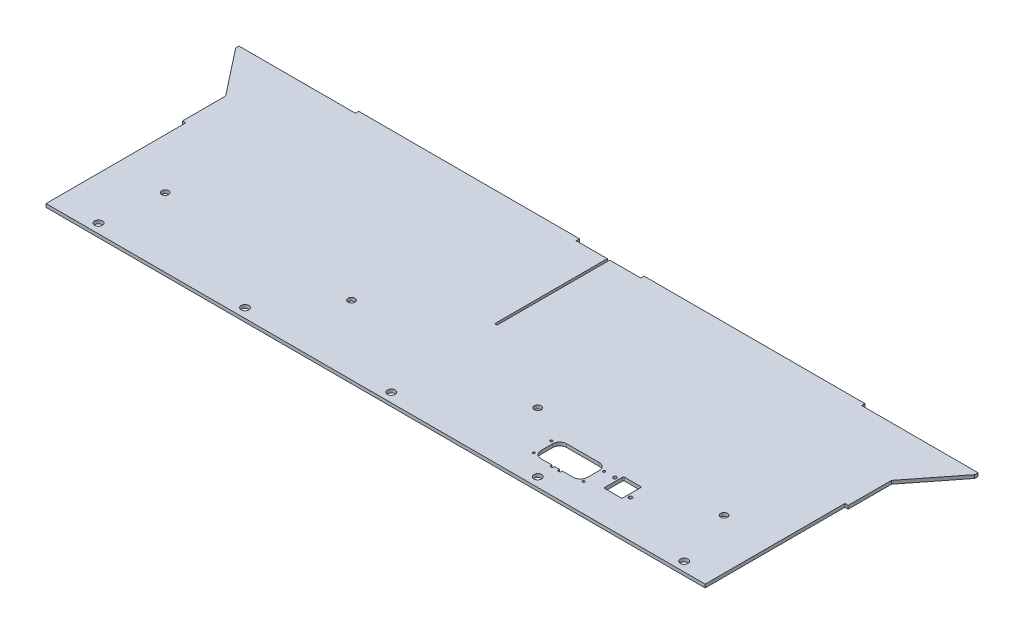
SolidWorks part; units mm, degrees
material "6061-T6 (SS)"
ref_plane "X-Y Datum" through (0, 0, 0) normal (0, 0, 1) x (1, 0, 0)
ref_plane "X-Z Datum" through (0, 0, 0) normal (0, 1, 0) x (1, 0, 0)
ref_plane "Y-Z Datum" through (0, 0, 0) normal (1, 0, 0) x (0, 0, -1)
sketch "Sketch1" plane through (0, 0, 0) normal (0, 1, 0) x (1, 0, 0)
  line L1 (-317.6778, 111.125) -> (317.6778, 111.125)
  line L2 (-317.6778, 111.125) -> (-317.6778, -111.125)
  line L3 (-317.6778, -111.125) -> (317.6778, -111.125)
  line L4 (317.6778, 111.125) -> (317.6778, -111.125)
  line L5 (-317.6778, 111.125) -> (317.6778, -111.125) construction
  line L6 (-317.6778, -111.125) -> (317.6778, 111.125) construction
  point P0 (0, 0)
  dimension "D1" = 635.3556
  dimension "D2" = 222.25
extrude "Boss-Extrude1" add sketch "Sketch1" along normal mid plane 3.175
sketch "Sketch3" plane through (0, 1.5875, 0) normal (0, 1, 0) x (1, 0, 0)
  line L0 (-317.6778, 111.125) -> (-352.6028, 111.125)
  line L1 (-352.6028, 111.125) -> (-352.6028, 107.95)
  line L2 (-352.6028, 107.95) -> (-317.6778, 63.5)
  line L3 (-317.6778, 111.125) -> (-317.6778, -111.125) construction
  line L16 (317.6778, -111.125) -> (317.6778, 111.125)
  line L17 (317.6778, 111.125) -> (-317.6778, 111.125)
  line L26 (-317.6778, 111.125) -> (-317.6778, -111.125)
  line L27 (-317.6778, -111.125) -> (317.6778, -111.125)
  line L38 (-317.6778, 111.125) -> (-317.6778, 63.5)
  line M26 (-317.6778, 111.125) -> (-317.6778, -111.125)
  dimension "D1" = 34.925
  dimension "D2" = 3.175
  dimension "D3" = 44.45
  dimension "D4" = 0
extrude "Boss-Extrude3" add sketch "Sketch3" against normal blind 3.175 contours L1 L2 L0 M26
mirror "Mirror1" about plane through (0, 0, 0) normal (1, 0, 0) of "Boss-Extrude3"
sketch "Sketch4" plane through (0, 1.5875, 0) normal (0, 1, 0) x (1, 0, 0)
  line L0 (-273.2278, -111.125) -> (-273.2278, -102.235)
  line L1 (-317.6778, -111.125) -> (317.6778, -111.125) construction
  line L2 (-273.2278, -102.235) -> (-317.6778, -102.235)
  line L3 (-317.6778, 63.5) -> (-317.6778, -111.125) construction
  circle A0 centre (-273.2278, -102.235) radius 3.675
extrude "Cut-Extrude1" cut sketch "Sketch4" against normal blind 10 contours L0 A0 L2 | L2 A0 L0
pattern_linear "LPattern1" count 5 spacing 139.7 along (1, 0, 0) of "Cut-Extrude1"
sketch "Sketch6" plane through (0, 1.5875, 0) normal (0, 1, 0) x (1, 0, 0)
  line L0 (0, -191.7444) -> (0, 191.7444) construction
  line L1 (317.6778, -111.125) -> (314.5028, -111.125)
  line L2 (317.6778, -111.125) -> (317.6778, 22.225)
  line L3 (317.6778, 22.225) -> (314.5028, 22.225)
  line L4 (314.5028, -111.125) -> (314.5028, 22.225)
  line L5 (-317.6778, -111.125) -> (-314.5028, -111.125)
  line L6 (-317.6778, 22.225) -> (-314.5028, 22.225)
  line L7 (-317.6778, -111.125) -> (-317.6778, 22.225)
  line L8 (-314.5028, -111.125) -> (-314.5028, 22.225)
  line L9 (352.6028, 111.125) -> (-352.6028, 111.125) construction
  line L10 (1.143, 111.125) -> (-1.143, 111.125)
  line L11 (1.143, 111.125) -> (1.143, 3.683)
  line L12 (1.143, 3.683) -> (-1.143, 3.683)
  line L13 (-1.143, 111.125) -> (-1.143, 3.683)
  line L14 (0, 3.683) -> (0, 111.125) construction
  point P9 (0, 0)
  dimension "D1" = 3.175
  dimension "D2" = 133.35
  dimension "D3" = 107.442
  dimension "D4" = 2.286
extrude "Cut-Extrude2" cut sketch "Sketch6" against normal through all
sketch "Sketch8" plane through (0, 1.5875, 0) normal (0, 1, 0) x (1, 0, 0)
  line L0 (-314.5028, -111.125) -> (314.5028, -111.125) construction
  line L1 (314.5028, 22.225) -> (314.5028, -111.125) construction
  circle A0 centre (266.7, -45.2374) radius 3
  dimension "D3" = 6
  dimension "D1" = 65.8876
  dimension "D2" = 47.8028
hole_wizard "M6 Clearance Hole1" positions "Sketch9" profile "Sketch10" hole size "M6" standard "ANSI Metric" end condition through all
sketch "Sketch9" plane through (0, 1.5875, 0) normal (0, 1, 0) x (1, 0, 0)
  point P0 (266.7, -45.2374)
sketch "Sketch10" plane through (266.7, 1.5875, 45.2374) normal (1, 0, 0) x (0, 0, 1)
  line L0 (0, 0) -> (0, 3.175)
  line L1 (0, 3.175) -> (3.3, 3.175)
  line L2 (3.3, 3.175) -> (3.3, 0)
  line L5 (3.3, 0) -> (0, 0)
  line L11 (0, -6.35) -> (0, 107.95) construction
  dimension "Thru Hole Dia." = 6.6
  dimension "Thru Hole Depth" = 3.175
pattern_linear "LPattern2" count 4 spacing 177.8 along (-1, 0, 0) of "M6 Clearance Hole1"
sketch "Sketch12" plane through (0, 0, -111.125) normal (0, 0, -1) x (-1, 0, 0)
  line L0 (-352.6028, -1.5875) -> (-1.143, -1.5875) construction
  line L1 (-241.4778, -1.5875) -> (-30.8229, -1.5875)
  line L2 (-241.4778, -1.5875) -> (-241.4778, 1.5875)
  line L3 (-241.4778, 1.5875) -> (-30.8229, 1.5875)
  line L4 (-30.8229, -1.5875) -> (-30.8229, 1.5875)
  line L5 (-241.4778, -1.5875) -> (-241.4778, 1.5875) construction
  line L6 (-352.6028, 1.5875) -> (-1.143, 1.5875) construction
  line L7 (-30.8229, 1.5875) -> (-30.8229, -1.5875) construction
  line L8 (1.143, 1.5875) -> (352.6028, 1.5875) construction
  line L9 (30.8229, 1.5875) -> (241.4778, 1.5875)
  line L10 (30.8229, 1.5875) -> (30.8229, -1.5875)
  line L11 (30.8229, -1.5875) -> (241.4778, -1.5875)
  line L12 (241.4778, 1.5875) -> (241.4778, -1.5875)
  line L13 (30.8229, 1.5875) -> (30.8229, -1.5875) construction
  line L14 (1.143, -1.5875) -> (352.6028, -1.5875) construction
  line L15 (241.4778, -1.5875) -> (241.4778, 1.5875) construction
extrude "Boss-Extrude4" add sketch "Sketch12" along normal blind 3.175
sketch "Sketch13" plane through (0, 1.5875, 0) normal (0, 1, 0) x (1, 0, 0)
  line L1 (145.2142, -85.2806) -> (143.4142, -85.2806) construction
  line L4 (152.4142, -85.2806) -> (150.6142, -85.2806) construction
  line L12 (145.4974, -87.7806) -> (145.7599, -84.7806) construction
  line L21 (143.131, -87.7806) -> (145.4974, -87.7806) construction
  line L22 (187.8642, -80.0254) -> (202.8142, -80.0254)
  line L23 (203.9642, -78.8754) -> (203.9642, -62.4254)
  line L28 (202.8142, -61.2754) -> (187.8642, -61.2754)
  line L29 (186.7142, -62.4254) -> (186.7142, -78.8754)
  line L30 (187.8642, -80.0254) -> (202.8142, -80.0254)
  line L45 (203.9642, -78.8754) -> (203.9642, -62.4254)
  line L46 (202.8142, -61.2754) -> (187.8642, -61.2754)
  line L47 (186.7142, -62.4254) -> (186.7142, -78.8754)
  line L60 (142.8686, -84.7806) -> (143.131, -87.7806) construction
  line L62 (152.4142, -85.7806) -> (163.4142, -85.7806) construction
  line L72 (170.1142, -79.0806) -> (170.1142, -67.8806) construction
  line L241 (163.4142, -61.1806) -> (132.4142, -61.1806) construction
  line L242 (125.7142, -67.8806) -> (125.7142, -79.0806) construction
  line L243 (132.4142, -85.7806) -> (143.4142, -85.7806) construction
  line L244 (202.8142, -79.5254) -> (202.8142, -78.8754) construction
  line L245 (152.6974, -87.7806) -> (152.9599, -84.7806) construction
  line L246 (150.331, -87.7806) -> (152.6974, -87.7806) construction
  line L247 (150.0686, -84.7806) -> (150.331, -87.7806) construction
  line L248 (145.2142, -85.7806) -> (150.6142, -85.7806) construction
  line L249 (145.2142, -85.2806) -> (143.4142, -85.2806)
  line L250 (152.4142, -85.2806) -> (150.6142, -85.2806)
  line L251 (145.4974, -87.7806) -> (145.7599, -84.7806)
  line L252 (143.131, -87.7806) -> (145.4974, -87.7806)
  line L253 (142.8686, -84.7806) -> (143.131, -87.7806)
  line L254 (152.4142, -85.7806) -> (163.4142, -85.7806)
  line L255 (170.1142, -79.0806) -> (170.1142, -67.8806)
  line L256 (163.4142, -61.1806) -> (132.4142, -61.1806)
  line L257 (125.7142, -67.8806) -> (125.7142, -79.0806)
  line L258 (132.4142, -85.7806) -> (143.4142, -85.7806)
  line L259 (202.8142, -79.5254) -> (202.8142, -78.8754)
  line L260 (152.6974, -87.7806) -> (152.9599, -84.7806)
  line L261 (150.331, -87.7806) -> (152.6974, -87.7806)
  line L262 (150.0686, -84.7806) -> (150.331, -87.7806)
  line L263 (145.2142, -85.7806) -> (150.6142, -85.7806)
  arc A72 (163.4142, -85.7806) -> (170.1142, -79.0806) centre (163.4142, -79.0806) ccw construction
  arc A73 (170.1142, -67.8806) -> (163.4142, -61.1806) centre (163.4142, -67.8806) ccw construction
  arc A74 (132.4142, -61.1806) -> (125.7142, -67.8806) centre (132.4142, -67.8806) ccw construction
  arc A75 (125.7142, -79.0806) -> (132.4142, -85.7806) centre (132.4142, -79.0806) ccw construction
  arc A76 (163.4142, -85.7806) -> (170.1142, -79.0806) centre (163.4142, -79.0806) ccw
  arc A77 (170.1142, -67.8806) -> (163.4142, -61.1806) centre (163.4142, -67.8806) ccw
  arc A78 (132.4142, -61.1806) -> (125.7142, -67.8806) centre (132.4142, -67.8806) ccw
  arc A79 (125.7142, -79.0806) -> (132.4142, -85.7806) centre (132.4142, -79.0806) ccw
  spline S8 degree 3 poles (-1500.8883, -4778.2266) (166.1174, 186.6721) (190.3999, -88.1059) (203.6527, -79.7139) (212.0447, -66.4612) (-62.7298, -42.1789) (4902.0719, 1624.7958) knots -23.26266 -23.26266 -23.26266 -23.26266 0.25 0.5 0.75 24.262513 24.262513 24.262513 24.262513 only from (202.8142, -80.0254) to (203.9642, -78.8754)
  spline S9 degree 3 poles (4902.1654, -1766.128) (-62.7333, -99.1222) (212.0448, -74.8397) (203.6527, -61.5869) (190.4, -53.1949) (166.1177, -327.9695) (-1500.8569, 4636.8323) knots -23.26266 -23.26266 -23.26266 -23.26266 0.25 0.5 0.75 24.262513 24.262513 24.262513 24.262513 only from (203.9642, -62.4254) to (202.8142, -61.2754)
  spline S10 degree 3 poles (1891.5668, 4636.9258) (224.5611, -327.9729) (200.2785, -53.1948) (187.0258, -61.5869) (178.6337, -74.8396) (453.4083, -99.1219) (-4511.3935, -1766.0966) knots -23.26266 -23.26266 -23.26266 -23.26266 0.25 0.5 0.75 24.262513 24.262513 24.262513 24.262513 only from (187.8642, -61.2754) to (186.7142, -62.4254)
  spline S11 degree 3 poles (-4511.487, 1624.8272) (453.4117, -42.1786) (178.6337, -66.4611) (187.0258, -79.7139) (200.2784, -88.1059) (224.5608, 186.6687) (1891.5354, -4778.1331) knots -23.26266 -23.26266 -23.26266 -23.26266 0.25 0.5 0.75 24.262513 24.262513 24.262513 24.262513 only from (186.7142, -78.8754) to (187.8642, -80.0254)
  spline S28 degree 3 poles (202.8142, -80.0254) (202.9579, -80.0254) (203.2388, -79.976) (203.6527, -79.7139) (203.9148, -79.2999) (203.9642, -79.019) (203.9642, -78.8754) knots 0 0 0 0 0.25 0.5 0.75 1 1 1 1
  spline S29 degree 3 poles (203.9642, -62.4254) (203.9642, -62.2817) (203.9148, -62.0009) (203.6527, -61.5869) (203.2388, -61.3248) (202.9579, -61.2754) (202.8142, -61.2754) knots 0 0 0 0 0.25 0.5 0.75 1 1 1 1
  spline S30 degree 3 poles (187.8642, -61.2754) (187.7206, -61.2754) (187.4397, -61.3248) (187.0258, -61.5869) (186.7636, -62.0009) (186.7142, -62.2817) (186.7142, -62.4254) knots 0 0 0 0 0.25 0.5 0.75 1 1 1 1
  spline S31 degree 3 poles (186.7142, -78.8754) (186.7142, -79.019) (186.7636, -79.2999) (187.0258, -79.7139) (187.4397, -79.976) (187.7206, -80.0254) (187.8642, -80.0254) knots 0 0 0 0 0.25 0.5 0.75 1 1 1 1
  spline S140 degree 3 poles (172.6992, -84.2806) (172.6992, -86.4506) (170.5292, -86.4506) (170.5292, -84.2806) knots 0 0 0 0 1 1 1 1 weights 1 0.333333 0.333333 1 construction
  spline S141 degree 3 poles (170.5292, -84.2806) (170.5292, -82.1106) (172.6992, -82.1106) (172.6992, -84.2806) knots 0 0 0 0 1 1 1 1 weights 1 0.333333 0.333333 1 construction
  spline S142 degree 3 poles (121.6292, -66.1806) (121.6292, -64.0106) (123.7992, -64.0106) (123.7992, -66.1806) knots 0 0 0 0 1 1 1 1 weights 1 0.333333 0.333333 1 construction
  spline S143 degree 3 poles (123.7992, -66.1806) (123.7992, -68.3506) (121.6292, -68.3506) (121.6292, -66.1806) knots 0 0 0 0 1 1 1 1 weights 1 0.333333 0.333333 1 construction
  spline S144 degree 3 poles (123.1292, -84.2806) (123.1292, -82.1106) (125.2992, -82.1106) (125.2992, -84.2806) knots 0 0 0 0 1 1 1 1 weights 1 0.333333 0.333333 1 construction
  spline S145 degree 3 poles (125.2992, -84.2806) (125.2992, -86.4506) (123.1292, -86.4506) (123.1292, -84.2806) knots 0 0 0 0 1 1 1 1 weights 1 0.333333 0.333333 1 construction
  spline S146 degree 3 poles (172.6992, -84.2806) (172.6992, -86.4506) (170.5292, -86.4506) (170.5292, -84.2806) knots 0 0 0 0 1 1 1 1 weights 1 0.333333 0.333333 1
  spline S147 degree 3 poles (170.5292, -84.2806) (170.5292, -82.1106) (172.6992, -82.1106) (172.6992, -84.2806) knots 0 0 0 0 1 1 1 1 weights 1 0.333333 0.333333 1
  spline S148 degree 3 poles (121.6292, -66.1806) (121.6292, -64.0106) (123.7992, -64.0106) (123.7992, -66.1806) knots 0 0 0 0 1 1 1 1 weights 1 0.333333 0.333333 1
  spline S149 degree 3 poles (123.7992, -66.1806) (123.7992, -68.3506) (121.6292, -68.3506) (121.6292, -66.1806) knots 0 0 0 0 1 1 1 1 weights 1 0.333333 0.333333 1
  spline S150 degree 3 poles (123.1292, -84.2806) (123.1292, -82.1106) (125.2992, -82.1106) (125.2992, -84.2806) knots 0 0 0 0 1 1 1 1 weights 1 0.333333 0.333333 1
  spline S151 degree 3 poles (125.2992, -84.2806) (125.2992, -86.4506) (123.1292, -86.4506) (123.1292, -84.2806) knots 0 0 0 0 1 1 1 1 weights 1 0.333333 0.333333 1
  spline S152 degree 3 poles (172.0292, -66.1806) (172.0292, -64.0106) (174.1992, -64.0106) (174.1992, -66.1806) knots 0 0 0 0 1 1 1 1 weights 1 0.333333 0.333333 1 construction
  spline S153 degree 3 poles (174.1992, -66.1806) (174.1992, -68.3506) (172.0292, -68.3506) (172.0292, -66.1806) knots 0 0 0 0 1 1 1 1 weights 1 0.333333 0.333333 1 construction
  spline S154 degree 3 poles (172.0292, -66.1806) (172.0292, -64.0106) (174.1992, -64.0106) (174.1992, -66.1806) knots 0 0 0 0 1 1 1 1 weights 1 0.333333 0.333333 1
  spline S155 degree 3 poles (174.1992, -66.1806) (174.1992, -68.3506) (172.0292, -68.3506) (172.0292, -66.1806) knots 0 0 0 0 1 1 1 1 weights 1 0.333333 0.333333 1
  spline S156 degree 3 poles (181.7392, -66.1504) (181.7392, -69.3504) (184.9392, -69.3504) (184.9392, -66.1504) (184.9392, -62.9504) (181.7392, -62.9504) (181.7392, -66.1504) (181.7392, -69.3504) (184.9392, -69.3504) knots -0.5 0 0 0 0.5 0.5 0.5 1 1 1 1.5 1.5 1.5 weights 1 0.333333 0.333333 1 0.333333 0.333333 1 0.333333 0.333333 only from (181.7392, -66.1504) to (181.7392, -66.1504) construction
  spline S157 degree 3 poles (205.7392, -75.1504) (205.7392, -78.3504) (208.9392, -78.3504) (208.9392, -75.1504) (208.9392, -71.9504) (205.7392, -71.9504) (205.7392, -75.1504) (205.7392, -78.3504) (208.9392, -78.3504) knots -0.5 0 0 0 0.5 0.5 0.5 1 1 1 1.5 1.5 1.5 weights 1 0.333333 0.333333 1 0.333333 0.333333 1 0.333333 0.333333 only from (205.7392, -75.1504) to (205.7392, -75.1504) construction
  spline S158 degree 3 poles (181.7392, -66.1504) (181.7392, -69.3504) (184.9392, -69.3504) (184.9392, -66.1504) (184.9392, -62.9504) (181.7392, -62.9504) (181.7392, -66.1504) (181.7392, -69.3504) (184.9392, -69.3504) knots -0.5 0 0 0 0.5 0.5 0.5 1 1 1 1.5 1.5 1.5 weights 1 0.333333 0.333333 1 0.333333 0.333333 1 0.333333 0.333333 only from (181.7392, -66.1504) to (181.7392, -66.1504)
  spline S159 degree 3 poles (205.7392, -75.1504) (205.7392, -78.3504) (208.9392, -78.3504) (208.9392, -75.1504) (208.9392, -71.9504) (205.7392, -71.9504) (205.7392, -75.1504) (205.7392, -78.3504) (208.9392, -78.3504) knots -0.5 0 0 0 0.5 0.5 0.5 1 1 1 1.5 1.5 1.5 weights 1 0.333333 0.333333 1 0.333333 0.333333 1 0.333333 0.333333 only from (205.7392, -75.1504) to (205.7392, -75.1504)
  dimension "D1" = 0
extrude "Cut-Extrude3" cut sketch "Sketch13" against normal through all
